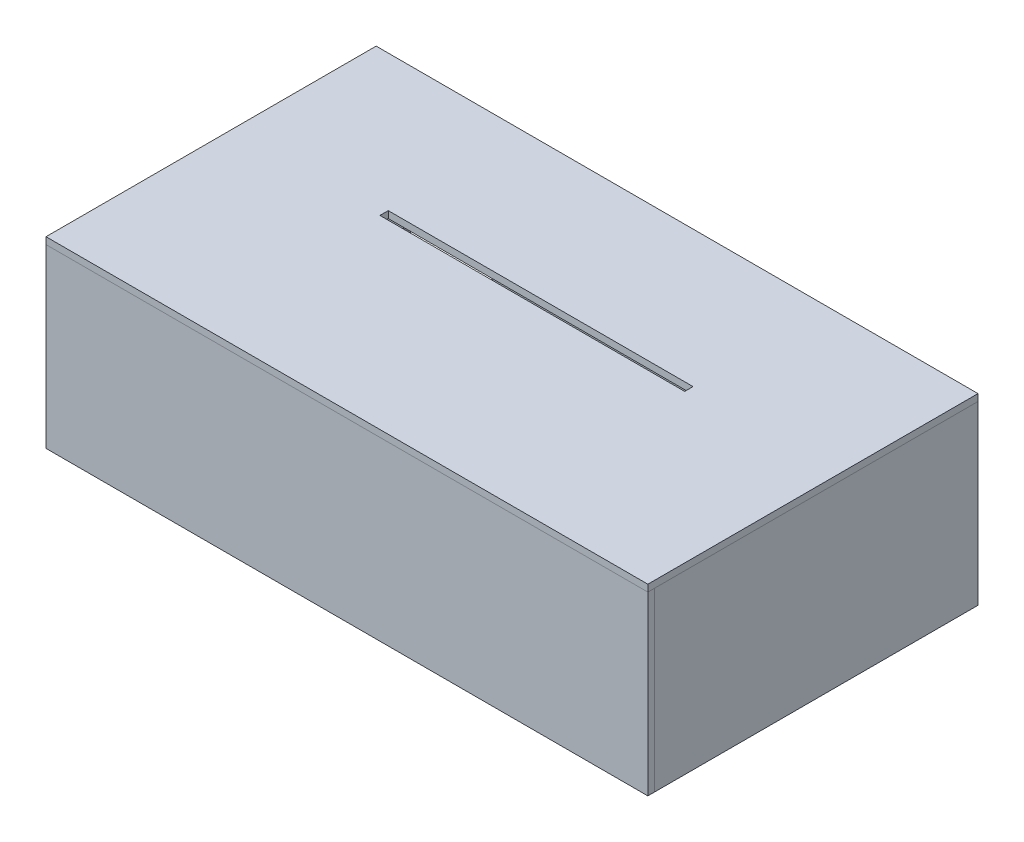
SolidWorks part; units mm, degrees
ref_plane "Front Plane" through (0, 0, 0) normal (0, 0, 1) x (1, 0, 0)
ref_plane "Top Plane" through (0, 0, 0) normal (0, 1, 0) x (1, 0, 0)
ref_plane "Right Plane" through (0, 0, 0) normal (1, 0, 0) x (0, 0, -1)
sketch "Sketch1" plane through (0, 0, 0) normal (0, 1, 0) x (1, 0, 0)
  line L1 (-228.854, -125.5395) -> (228.854, -125.5395)
  line L2 (-228.854, -125.5395) -> (-228.854, 125.5395)
  line L3 (-228.854, 125.5395) -> (228.854, 125.5395)
  line L4 (228.854, -125.5395) -> (228.854, 125.5395)
  line L5 (-228.854, -125.5395) -> (228.854, 125.5395) construction
  line L6 (-228.854, 125.5395) -> (228.854, -125.5395) construction
  point P0 (0, 0)
  dimension "D1" = 457.708
  dimension "D2" = 251.079
extrude "Boss-Extrude1" add sketch "Sketch1" along normal blind 5.207
sketch "Sketch2" plane through (0, 0, 125.5395) normal (0, 0, 1) x (1, 0, 0)
  line L0 (118.4275, -124.714) -> (223.0755, -124.714) construction
  line L1 (-228.854, 0) -> (228.854, 0)
  line L2 (-228.854, 0) -> (-228.854, -134.239)
  line L3 (-228.854, -134.239) -> (228.854, -134.239)
  line L4 (228.854, 0) -> (228.854, -134.239)
  dimension "D1" = 9.525
extrude "Boss-Extrude2" add sketch "Sketch2" against normal blind 5.207 separate body
sketch "Sketch4" plane through (0, 0, 0) normal (1, 0, 0) x (0, 0, -1)
  line L0 (-125.5395, -134.239) -> (-120.3325, -129.032)
  line L1 (-120.3325, -134.239) -> (-120.3325, 0) construction
  line L2 (-120.3325, -129.032) -> (-120.3325, -134.239)
  line L3 (-120.3325, -134.239) -> (-125.5395, -134.239)
  dimension "D1" = 45
extrude "Cut-Extrude1" cut sketch "Sketch4" against normal mid plane 234.95
sketch "Sketch3" plane through (-228.854, 0, 0) normal (1, 0, 0) x (0, 0, -1)
  line L0 (-120.3325, -134.239) -> (-120.3325, 0) construction
  line L1 (-120.3325, 0) -> (125.5395, 0)
  line L2 (-120.3325, 0) -> (-120.3325, -134.239)
  line L3 (-120.3325, -134.239) -> (125.5395, -134.239)
  line L4 (125.5395, 0) -> (125.5395, -134.239)
  line L6 (-120.3325, -134.239) -> (-125.5395, -134.239) construction
extrude "Boss-Extrude5" add sketch "Sketch3" along normal blind 5.207 separate body
mirror "Mirror1" about plane through (0, 0, 0) normal (1, 0, 0) of bodies 103
sketch "Sketch5" plane through (0, 5.207, 0) normal (0, 1, 0) x (1, 0, 0)
  line L0 (-115.0937, 21.7805) -> (115.0938, 21.7805) construction
  line L1 (115.8875, 15.4305) -> (-115.8875, 15.4305)
  line L2 (115.8875, 15.4305) -> (115.8875, 21.7805)
  line L3 (115.8875, 21.7805) -> (-115.8875, 21.7805)
  line L4 (-115.8875, 15.4305) -> (-115.8875, 21.7805)
  line L5 (115.8875, 20.9867) -> (115.8875, 10.668) construction
  line L6 (-115.8875, 10.668) -> (-115.8875, 20.9867) construction
  line L7 (-115.8875, 15.4305) -> (115.8875, 15.4305) construction
extrude "Cut-Extrude2" cut sketch "Sketch5" against normal through all
sketch "Sketch6" plane through (0, 0, -125.5395) normal (0, 0, -1) x (-1, 0, 0)
  line L0 (190.7801, -42.8364) -> (147.6749, -85.9416) construction
  line L1 (-223.647, 0) -> (223.647, 0)
  line L2 (-223.647, 0) -> (-223.647, -134.239)
  line L3 (-223.647, -134.239) -> (223.647, -134.239)
  line L4 (223.647, 0) -> (223.647, -134.239)
  line L5 (200.5661, -52.6224) -> (180.9941, -33.0504) construction
  line L6 (137.8889, -76.1556) -> (157.4609, -95.7276) construction
  line L7 (202.8825, -64.389) -> (202.8825, -112.014)
  line L8 (196.5325, -118.364) -> (141.9225, -118.364)
  line L9 (135.5725, -112.014) -> (135.5725, -64.389)
  arc A0 (202.8825, -64.389) -> (135.5725, -64.389) centre (169.2275, -64.389) ccw
  arc A2 (155.8932, -34.8902) -> (153.1991, -37.5843) centre (154.5461, -36.2373) ccw construction
  arc A3 (141.9225, -118.364) -> (135.5725, -112.014) centre (141.9225, -112.014) cw
  arc A4 (202.8825, -112.014) -> (196.5325, -118.364) centre (196.5325, -112.014) cw
  point P14 (169.2275, -64.389)
  dimension "D1" = 6.35
  dimension "D2" = 15.875
extrude "Boss-Extrude6" add sketch "Sketch6" against normal blind 5.207 separate body
sketch "Sketch7" plane through (0, 0, -125.5395) normal (0, 0, -1) x (-1, 0, 0)
  line L0 (223.647, -134.239) -> (223.647, 0) construction
  line L1 (221.107, -2.54) -> (223.647, -2.54)
  line L2 (221.107, -2.54) -> (221.107, -2.794)
  line L3 (221.107, -2.794) -> (223.647, -2.794)
  line L4 (223.647, -2.54) -> (223.647, -2.794)
  line L5 (-228.854, 0) -> (228.854, 0) construction
  line L6 (0, 0) -> (0, -185.1824) construction
  line L7 (-223.647, -2.54) -> (-223.647, -2.794)
  line L8 (-221.107, -2.794) -> (-223.647, -2.794)
  line L9 (-221.107, -2.54) -> (-221.107, -2.794)
  line L10 (-221.107, -2.54) -> (-223.647, -2.54)
  dimension "D1" = 2.54
  dimension "D2" = 0.254
  dimension "D3" = 2.54
extrude "Cut-Extrude3" cut sketch "Sketch7" against normal blind 5.207
